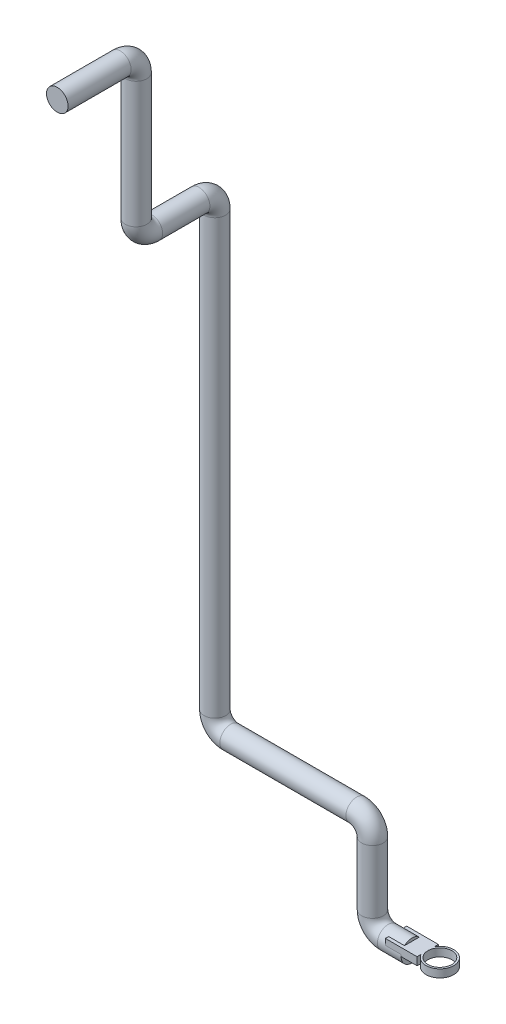
SolidWorks part; units mm, degrees
ref_plane "Alzado" through (0, 0, 0) normal (0, 0, 1) x (1, 0, 0)
ref_plane "Planta" through (0, 0, 0) normal (0, 1, 0) x (1, 0, 0)
ref_plane "Vista lateral" through (0, 0, 0) normal (1, 0, 0) x (0, 0, -1)
sketch3d "Croquis3D1"
  line L0 (0, 0, 0) -> (-30, 0, 0)
  line L1 (-50, 20, 0) -> (-50, 100, 0)
  line L2 (-70, 120, 0) -> (-230, 120, 0)
  line L3 (-250, 140, 0) -> (-250, 689.98, 0)
  line L4 (-250, 709.98, 20) -> (-250, 709.98, 80)
  line L5 (-250, 729.98, 100) -> (-250, 889.98, 100)
  line L6 (-250, 909.98, 120) -> (-250, 909.98, 200)
  arc A0 (-250, 889.98, 100) -> (-250, 909.98, 120) centre (-250, 889.98, 120) ccw
  arc A1 (-250, 709.98, 80) -> (-250, 729.98, 100) centre (-250, 729.98, 80) ccw
  arc A2 (-250, 689.98, 0) -> (-250, 709.98, 20) centre (-250, 689.98, 20) ccw
  arc A3 (-230, 120, 0) -> (-250, 140, 0) centre (-230, 140, 0) ccw
  arc A4 (-50, 100, 0) -> (-70, 120, 0) centre (-70, 100, 0) ccw
  arc A5 (-30, 0, 0) -> (-50, 20, 0) centre (-30, 20, 0) ccw
  point P12 (-250, 909.98, 100)
  point P13 (-230, 889.98, 120)
  point P16 (-250, 709.98, 100)
  point P17 (-270, 729.98, 80)
  point P20 (-250, 709.98, 0)
  point P21 (-230, 689.98, 20)
  point P24 (-250, 120, 0)
  point P25 (-230, 140, -20)
  point P28 (-50, 120, 0)
  point P29 (-70, 100, 20)
  point P32 (-50, 0, 0)
  point P33 (-30, 20, -20)
  dimension "D8" = 20
  dimension "D1" = 50
  dimension "D2" = 120
  dimension "D3" = 200
  dimension "D4" = 589.98
  dimension "D5" = 100
  dimension "D6" = 200
  dimension "D7" = 100
sketch "Croquis1" plane through (0, 0, 0) normal (1, 0, 0) x (0, 0, -1)
  circle A0 centre (0, 0) radius 13.7
  dimension "D1" = 27.4
sweep "Barrer1" add profiles "Croquis1" path "Croquis3D1"
ref_plane "Plano1" through (0, 0, 0) normal (1, 0, 0) x (0, 0, -1)
sketch "Croquis2" plane through (0, 0, 0) normal (0, 1, 0) x (1, 0, 0)
  line L0 (0, 0) -> (35.5498, 0)
  circle A0 centre (35.5498, 0) radius 15.1838
  circle A1 centre (35.5498, 0) radius 17.5986
extrude "Saliente-Extruir1" add sketch "Croquis2" along normal blind 10 separate body
sketch "Croquis3" plane through (0, 0, 0) normal (0, 1, 0) x (1, 0, 0)
  line L1 (-20.1081, 13.5124) -> (20.1081, 13.5124)
  line L2 (-20.1081, 13.5124) -> (-20.1081, -13.5124)
  line L3 (-20.1081, -13.5124) -> (20.1081, -13.5124)
  line L4 (20.1081, 13.5124) -> (20.1081, -13.5124)
  line L5 (-20.1081, 13.5124) -> (20.1081, -13.5124) construction
  line L6 (-20.1081, -13.5124) -> (20.1081, 13.5124) construction
  point P0 (0, 0)
extrude "Saliente-Extruir2" add sketch "Croquis3" along normal blind 10
